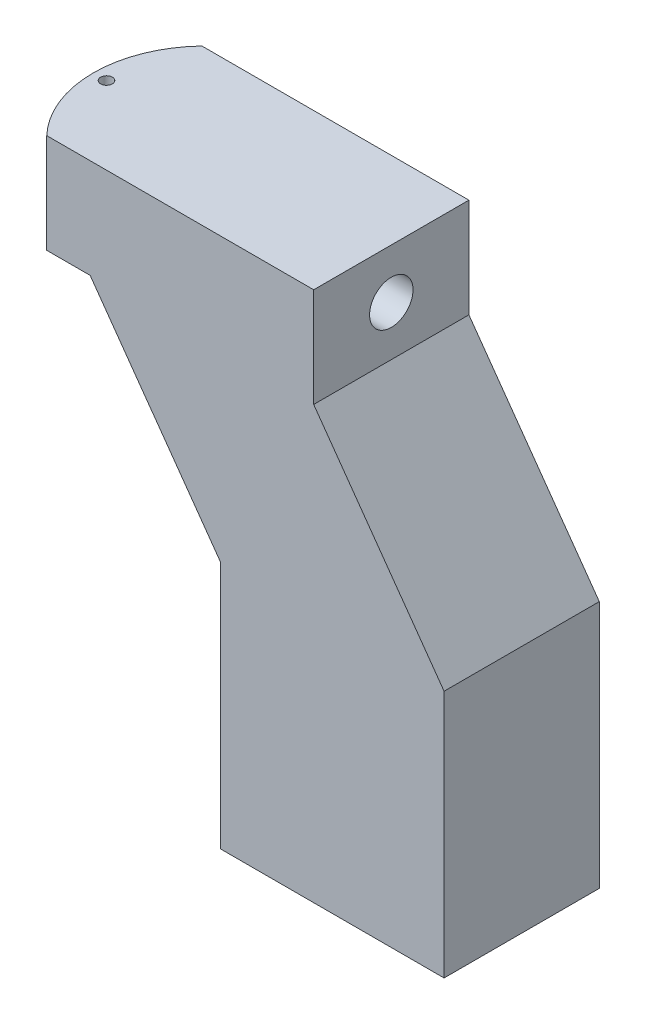
SolidWorks part; units mm, degrees
ref_plane "Front Plane" through (0, 0, 0) normal (0, 0, 1) x (1, 0, 0)
ref_plane "Top Plane" through (0, 0, 0) normal (0, 1, 0) x (1, 0, 0)
ref_plane "Right Plane" through (0, 0, 0) normal (1, 0, 0) x (0, 0, -1)
sketch "Sketch1" plane through (0, 0, 0) normal (0, 0, 1) x (1, 0, 0)
  line L0 (0, 0) -> (12.192, 0)
  line L1 (12.192, 0) -> (12.192, -4.064)
  line L2 (8.382, -21.717) -> (17.526, -21.717)
  line L3 (0, 0) -> (0, -4.064)
  line L4 (8.382, -11.557) -> (8.382, -21.717)
  line L5 (17.526, -11.557) -> (17.526, -21.717)
  line L6 (3.048, -4.064) -> (8.382, -11.557)
  line L7 (12.192, -4.064) -> (17.526, -11.557)
  line L8 (0, -4.064) -> (3.048, -4.064)
  dimension "D1" = 4.064
  dimension "D2" = 12.192
  dimension "D3" = 21.717
  dimension "D4" = 8.382
  dimension "D5" = 9.144
  dimension "D6" = 7.493
  dimension "D7" = 3.048
extrude "Boss-Extrude1" add sketch "Sketch1" against normal blind 6.35
sketch "Sketch2" plane through (0, 0, 0) normal (0, 1, 0) x (1, 0, 0)
  line L0 (1.27, 6.35) -> (1.27, 0) construction
  line L1 (12.192, 6.35) -> (0, 6.35) construction
  line L2 (12.192, 0) -> (0, 0) construction
  line L3 (0, 6.35) -> (0, 0) construction
  line L4 (1.27, 6.35) -> (-1.3329, 6.35)
  line L6 (-1.3329, 0) -> (1.27, 0)
  line L7 (-1.3329, 6.35) -> (-1.3329, 0)
  arc A0 (1.27, 6.35) -> (1.27, 0) centre (4.6038, 3.175) ccw
  dimension "D1" = 1.27
extrude "Cut-Extrude1" cut sketch "Sketch2" against normal blind 6.35
sketch "Sketch3" plane through (12.192, 0, 0) normal (1, 0, 0) x (0, 0, -1)
  line L0 (6.35, -4.064) -> (0, -4.064) construction
  circle A0 centre (3.175, -2.032) radius 0.889
  point P5 (3.175, -4.064)
  dimension "D1" = 1.778
  dimension "D2" = 2.032
sketch "Sketch5" plane through (0, -21.717, 0) normal (0, -1, 0) x (1, 0, 0)
  line L0 (8.382, 0) -> (17.526, -6.35) construction
  line L1 (17.526, 0) -> (8.382, -6.35) construction
  circle A0 centre (12.954, -3.175) radius 1.5875
  dimension "D1" = 3.175
extrude "Cut-Extrude4" cut sketch "Sketch5" against normal blind 7.62
sketch "Sketch6" plane through (0, 0, 0) normal (0, 1, 0) x (1, 0, 0)
  line L0 (0, 0) -> (0, 8.7102) construction
  line L2 (0, 3.175) -> (12.192, 3.175) construction
  line L3 (12.192, 2.286) -> (12.192, 4.064) construction
  arc A0 (1.27, 6.35) -> (1.27, 0) centre (4.6038, 3.175) ccw construction
sketch "Sketch7" plane through (0, 0, 0) normal (0, 1, 0) x (1, 0, 0)
  line L0 (0, 3.175) -> (12.192, 3.175) construction
  circle A0 centre (0.541, 3.175) radius 0.24
  dimension "D1" = 0.4801
  dimension "D2" = 0.541
extrude "Cut-Extrude5" cut sketch "Sketch7" against normal through all
hole_wizard "#2-56 Tapped Hole1" positions "Sketch8" profile "Sketch10" tap size "#2-56" standard "ANSI Inch" end condition through all
sketch "Sketch8" plane through (12.192, 0, 0) normal (1, 0, 0) x (0, 0, -1)
  point P0 (3.175, -2.032)
sketch "Sketch10" plane through (12.192, -2.032, -3.175) normal (0, 1, 0) x (0, 0, -1)
  line L0 (0, 0) -> (0, 12.192)
  line L1 (0, 12.192) -> (0.889, 12.192)
  line L2 (0.889, 12.192) -> (0.889, 0)
  line L5 (0.889, 0) -> (0, 0)
  line L11 (0, -6.35) -> (0, 107.95) construction
  dimension "Thru Tap Drill Dia." = 1.778
  dimension "Thru Tap Drill Depth" = 12.192
cosmetic thread "Hole Thread1" parameters "D2"=2.1844
